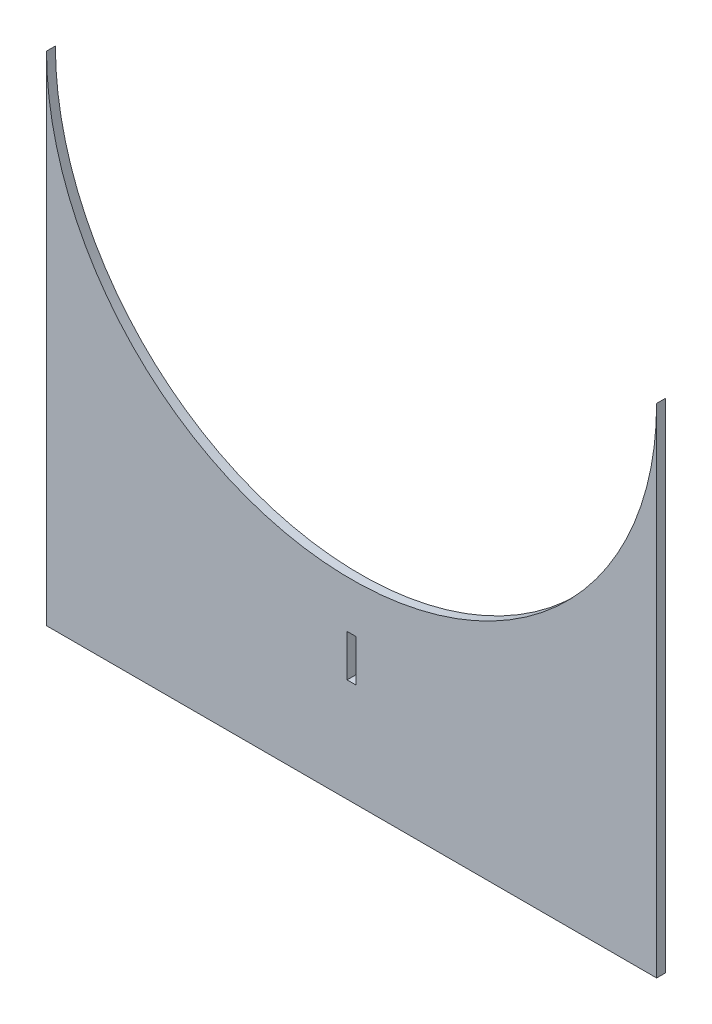
SolidWorks part; units mm, degrees
ref_plane "Front Plane" through (0, 0, 0) normal (0, 0, 1) x (1, 0, 0)
ref_plane "Top Plane" through (0, 0, 0) normal (0, 1, 0) x (1, 0, 0)
ref_plane "Right Plane" through (0, 0, 0) normal (1, 0, 0) x (0, 0, -1)
sketch "Sketch1" plane through (0, 0, 0) normal (0, 0, 1) x (1, 0, 0)
  line L1 (-109, -88.9) -> (109, -88.9)
  line L2 (-109, -88.9) -> (-109, 88.9)
  line L3 (-109, 88.9) -> (109, 88.9)
  line L4 (109, -88.9) -> (109, 88.9)
  line L5 (-109, -88.9) -> (109, 88.9) construction
  line L6 (-109, 88.9) -> (109, -88.9) construction
  arc A0 (-109, 88.9) -> (109, 88.9) centre (0, 88.9) ccw
  point P0 (0, 0)
  dimension "D1" = 109
  dimension "D2" = 177.8
extrude "Boss-Extrude1" add sketch "Sketch1" along normal blind 3.175 contours A0 L2 L1 L4
sketch "Sketch2" plane through (0, 0, 0) normal (0, 0, -1) x (-1, 0, 0)
  line L0 (0, 0) -> (0, -88.9) construction
  line L1 (109, -88.9) -> (-109, -88.9) construction
  line L3 (-1.5875, -36.95) -> (1.5875, -36.95)
  line L4 (-1.5875, -36.95) -> (-1.5875, -51.95)
  line L5 (-1.5875, -51.95) -> (1.5875, -51.95)
  line L6 (1.5875, -36.95) -> (1.5875, -51.95)
  line L7 (-1.5875, -36.95) -> (1.5875, -51.95) construction
  line L8 (-1.5875, -51.95) -> (1.5875, -36.95) construction
  point P5 (0, -44.45)
  dimension "D1" = 3.175
  dimension "D2" = 15
extrude "Cut-Extrude1" cut sketch "Sketch2" against normal blind 3.175
